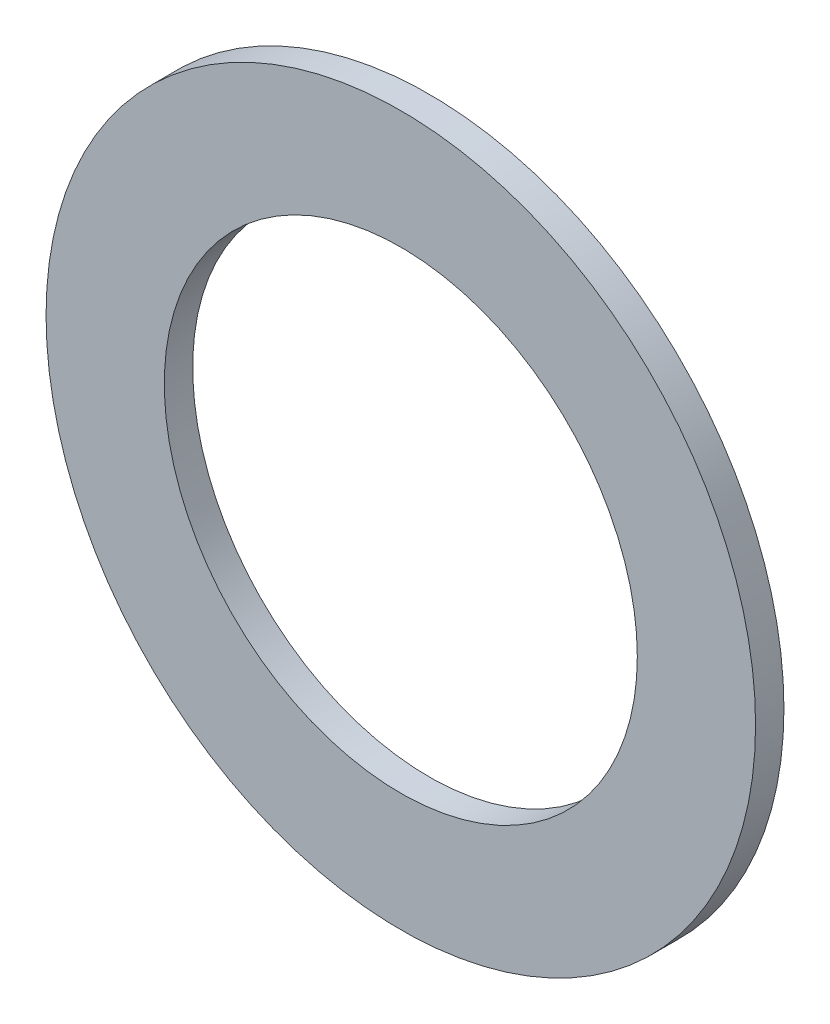
SolidWorks part; units mm, degrees
material "AISI 316 Stainless Steel Sheet (SS)"
ref_plane "Front Plane" through (0, 0, 0) normal (0, 0, 1) x (1, 0, 0)
ref_plane "Top Plane" through (0, 0, 0) normal (0, 1, 0) x (1, 0, 0)
ref_plane "Right Plane" through (0, 0, 0) normal (1, 0, 0) x (0, 0, -1)
sketch "Sketch1" plane through (0, 0, 0) normal (0, 0, 1) x (1, 0, 0)
  circle A0 centre (0, 0) radius 6.35
  circle A1 centre (0, 0) radius 9.525
  dimension "D1" = 19.05
  dimension "D2" = 12.7
extrude "Boss-Extrude1" add sketch "Sketch1" along normal blind 0.762
